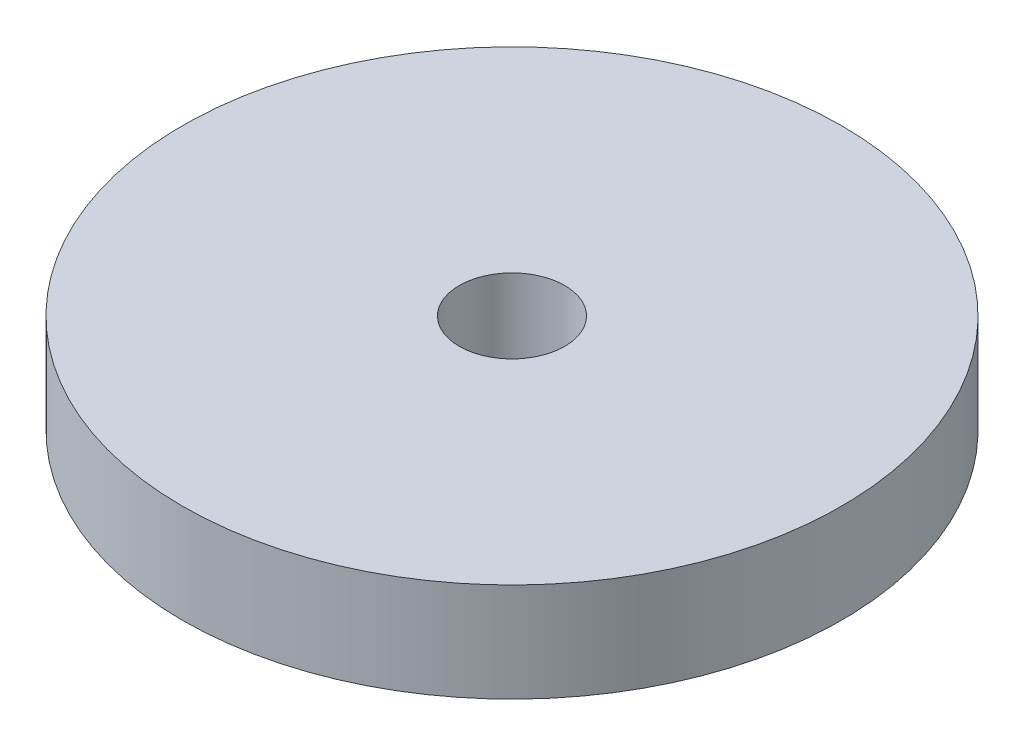
SolidWorks part; units mm, degrees
ref_plane "Front Plane" through (0, 0, 0) normal (0, 0, 1) x (1, 0, 0)
ref_plane "Top Plane" through (0, 0, 0) normal (0, 1, 0) x (1, 0, 0)
ref_plane "Right Plane" through (0, 0, 0) normal (1, 0, 0) x (0, 0, -1)
sketch "Sketch1" plane through (0, 0, 0) normal (0, 1, 0) x (1, 0, 0)
  circle A0 centre (0, 0) radius 10
  circle A1 centre (0, 0) radius 1.6
  dimension "D1" = 3.2
  dimension "D2" = 20
extrude "Boss-Extrude1" add sketch "Sketch1" along normal blind 3
